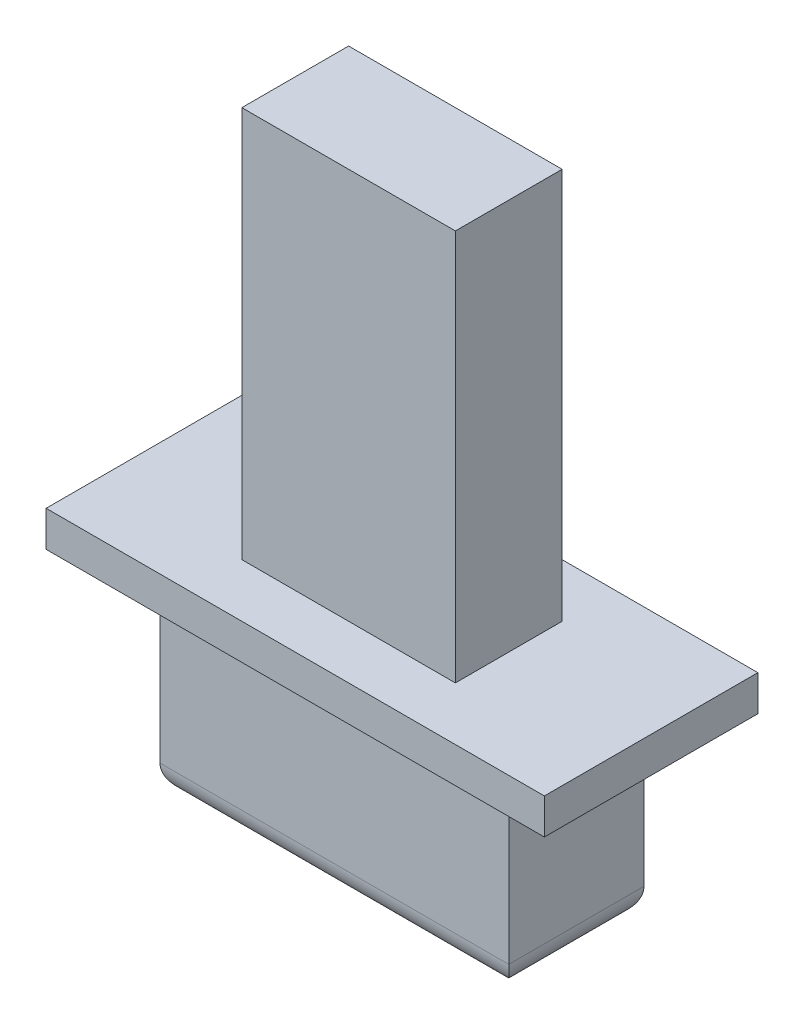
SolidWorks part; units mm, degrees
ref_plane "Front Plane" through (0, 0, 0) normal (0, 0, 1) x (1, 0, 0)
ref_plane "Top Plane" through (0, 0, 0) normal (0, 1, 0) x (1, 0, 0)
ref_plane "Right Plane" through (0, 0, 0) normal (1, 0, 0) x (0, 0, -1)
sketch "Sketch1" plane through (0, 0, 0) normal (0, 1, 0) x (1, 0, 0)
  line L1 (2.45, -0.95) -> (-2.45, -0.95)
  line L2 (2.45, -0.95) -> (2.45, 0.95)
  line L3 (2.45, 0.95) -> (-2.45, 0.95)
  line L4 (-2.45, -0.95) -> (-2.45, 0.95)
  line L5 (2.45, -0.95) -> (-2.45, 0.95) construction
  line L6 (2.45, 0.95) -> (-2.45, -0.95) construction
  point P0 (0, 0)
  dimension "D1" = 4.9
  dimension "D2" = 1.9
extrude "Boss-Extrude1" add sketch "Sketch1" along normal blind 2.75
sketch "Sketch2" plane through (0, 2.75, 0) normal (0, 1, 0) x (1, 0, 0)
  line L1 (1.5, 0.75) -> (-1.5, 0.75)
  line L2 (1.5, 0.75) -> (1.5, -0.75)
  line L3 (1.5, -0.75) -> (-1.5, -0.75)
  line L4 (-1.5, 0.75) -> (-1.5, -0.75)
  line L5 (1.5, 0.75) -> (-1.5, -0.75) construction
  line L6 (1.5, -0.75) -> (-1.5, 0.75) construction
  point P0 (0, 0)
  dimension "D1" = 3
  dimension "D2" = 1.5
extrude "Boss-Extrude2" add sketch "Sketch2" along normal blind 6
fillet "Fillet2" radius 0.4 4 edges at (0, 0, 0.95) (2.45, 0, 0) (0, 0, -0.95) (-2.45, 0, 0)
sketch "Sketch3" plane through (0, 2.75, 0) normal (0, 1, 0) x (1, 0, 0)
  line L1 (-3.5, -1.5) -> (3.5, -1.5)
  line L2 (-3.5, -1.5) -> (-3.5, 1.5)
  line L3 (-3.5, 1.5) -> (3.5, 1.5)
  line L4 (3.5, -1.5) -> (3.5, 1.5)
  line L5 (-3.5, -1.5) -> (3.5, 1.5) construction
  line L6 (-3.5, 1.5) -> (3.5, -1.5) construction
  point P0 (0, 0)
  dimension "D1" = 7
  dimension "D2" = 3
extrude "Boss-Extrude3" add sketch "Sketch3" along normal blind 0.5 separate body
